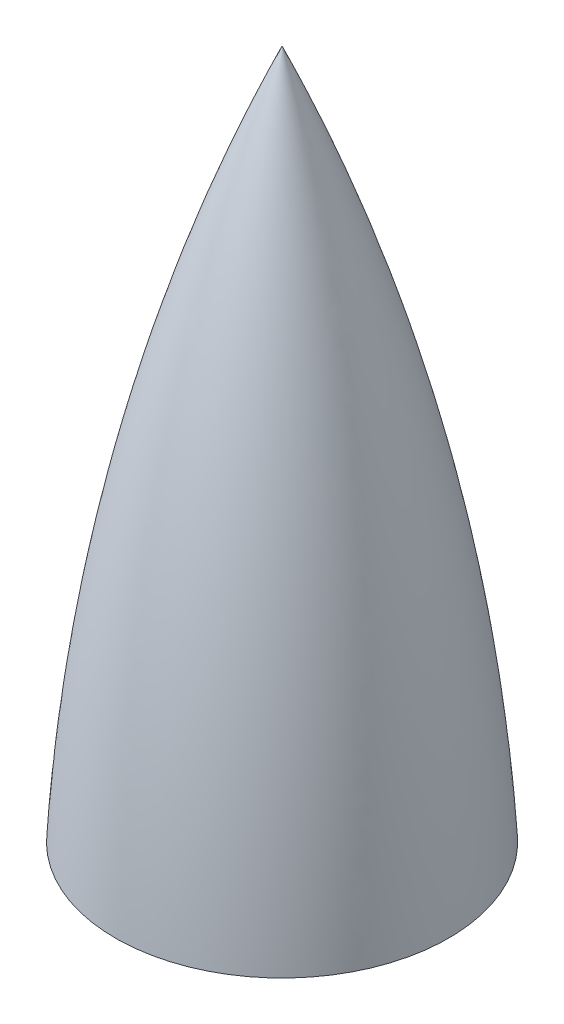
SolidWorks part; units mm, degrees
material "PVB"
ref_plane "Front Plane" through (0, 0, 0) normal (0, 0, 1) x (1, 0, 0)
ref_plane "Top Plane" through (0, 0, 0) normal (0, 1, 0) x (1, 0, 0)
ref_plane "Right Plane" through (0, 0, 0) normal (1, 0, 0) x (0, 0, -1)
sketch "Sketch2" plane through (0, 0, 0) normal (0, 0, 1) x (1, 0, 0)
  line L0 (0, 0) -> (0, 381) construction
  line L1 (-92.075, 0) -> (-88.9, 0)
  line L2 (0, 381) -> (0, 375.92)
  arc A0 (0, 381) -> (-92.075, 0) centre (999.5165, -62.1756) ccw
  arc A1 (0, 375.92) -> (-88.9, 0) centre (1114.6958, -86.1623) ccw
  dimension "D1" = 381
  dimension "D2" = 5.08
  dimension "D4" = 88.9
  dimension "D3" = 92.075
revolve "Revolve1" add sketch "Sketch2" angle 360 about L2
sketch "Sketch3" plane through (0, 0, 0) normal (0, -1, 0) x (1, 0, 0)
  circle A0 centre (0, 0) radius 88.9
  circle A1 centre (0, 0) radius 86.995
  dimension "D1" = 177.8
extrude "Boss-Extrude1" [suppressed] add sketch "Sketch3" along normal blind 35.56
equation "\"D4@Sketch2\"=3.5"
